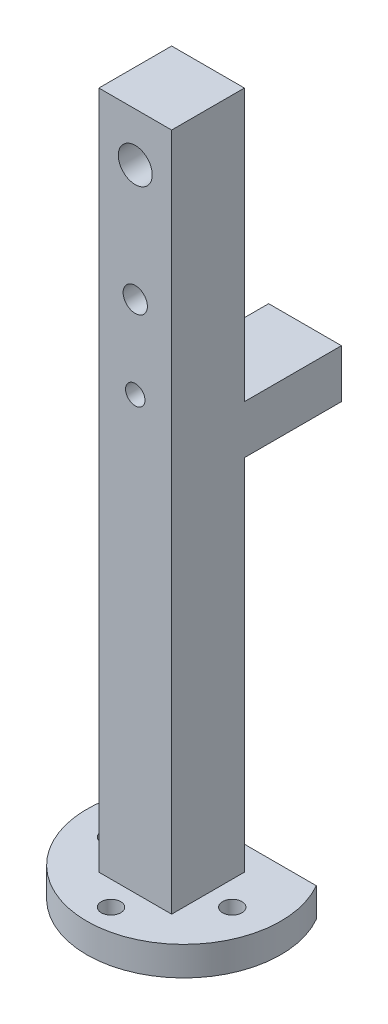
SolidWorks part; units mm, degrees
material "Oak"
ref_plane "Front Plane" through (0, 0, 0) normal (0, 0, 1) x (1, 0, 0)
ref_plane "Top Plane" through (0, 0, 0) normal (0, 1, 0) x (1, 0, 0)
ref_plane "Right Plane" through (0, 0, 0) normal (1, 0, 0) x (0, 0, -1)
sketch "Sketch1" plane through (0, 0, 0) normal (0, 1, 0) x (1, 0, 0)
  line L1 (0, 19.05) -> (19.05, 19.05)
  line L2 (0, 19.05) -> (0, 0)
  line L3 (0, 0) -> (19.05, 0)
  line L4 (19.05, 19.05) -> (19.05, 0)
  dimension "D1" = 19.05
  dimension "D2" = 19.05
extrude "Boss-Extrude1" add sketch "Sketch1" along normal blind 177.8
sketch "Sketch2" plane through (0, 0, 0) normal (0, -1, 0) x (1, 0, 0)
  line L2 (19.05, -19.05) -> (0, -19.05) construction
  line L3 (19.05, 0) -> (19.05, -19.05) construction
  line L4 (-12.472, -25.4) -> (31.522, -25.4)
  circle A0 centre (9.525, -12.7) radius 25.4
  dimension "D1" = 50.8
  dimension "D2" = 6.35
  dimension "D3" = 9.525
  dimension "D4" = 6.35
extrude "Boss-Extrude2" add sketch "Sketch2" along normal blind 7.62
sketch "Sketch3" plane through (0, 0, 0) normal (0, 1, 0) x (1, 0, 0)
  line L0 (0, 0) -> (19.05, 0) construction
  line L1 (0, 19.05) -> (0, 0) construction
  line L2 (19.05, 0) -> (19.05, 19.05) construction
  line L3 (0, 0) -> (19.05, 0) construction
  line L4 (19.05, 0) -> (19.05, 19.05) construction
  circle A0 centre (-6.35, 9.525) radius 2.54
  circle A1 centre (25.4, 9.525) radius 2.54
  circle A2 centre (9.525, -6.35) radius 2.54
  dimension "D1" = 5.08
  dimension "D2" = 5.08
  dimension "D3" = 5.08
  dimension "D5" = 6.35
  dimension "D6" = 6.35
  dimension "D4" = 6.35
  dimension "D7" = 9.525
  dimension "D8" = 9.525
  dimension "D9" = 9.525
extrude "Cut-Extrude1" cut sketch "Sketch3" against normal blind 7.62
sketch "Sketch4" plane through (0, 0, -19.05) normal (0, 0, -1) x (-1, 0, 0)
  line L0 (-19.05, 177.8) -> (-19.05, 0) construction
  line L2 (-19.05, 177.8) -> (0, 177.8) construction
  circle A0 centre (-9.525, 165.1) radius 4.445
  dimension "D1" = 8.89
  dimension "D2" = 9.525
  dimension "D3" = 12.7
extrude "Cut-Extrude2" cut sketch "Sketch4" against normal blind 19.05
sketch "Sketch5" plane through (0, 0, -19.05) normal (0, 0, -1) x (-1, 0, 0)
  line L0 (-9.525, 191.3388) -> (-9.525, 109.2447) construction
  circle A0 centre (-9.525, 165.1) radius 4.445 construction
  circle A1 centre (-9.525, 165.1) radius 4.445
  circle A2 centre (-9.525, 134.62) radius 3.175
  circle A3 centre (-9.525, 113.03) radius 2.54
  dimension "D1" = 30.48
  dimension "D2" = 6.35
  dimension "D3" = 21.59
  dimension "D4" = 5.08
extrude "Cut-Extrude3" cut sketch "Sketch5" against normal blind 38.1 contours A2 | A3
sketch "Sketch6" plane through (0, 0, -19.05) normal (0, 0, -1) x (-1, 0, 0)
  line L0 (-19.05, 177.8) -> (-19.05, 0) construction
  line L1 (-19.05, 106.68) -> (0, 106.68)
  line L2 (-19.05, 106.68) -> (-19.05, 93.98)
  line L3 (-19.05, 93.98) -> (0, 93.98)
  line L4 (0, 106.68) -> (0, 93.98)
  line L5 (0, 177.8) -> (0, 0) construction
  line L6 (-19.05, 0) -> (0, 0) construction
  dimension "D1" = 12.7
  dimension "D2" = 106.68
extrude "Boss-Extrude3" add sketch "Sketch6" along normal blind 25.4
